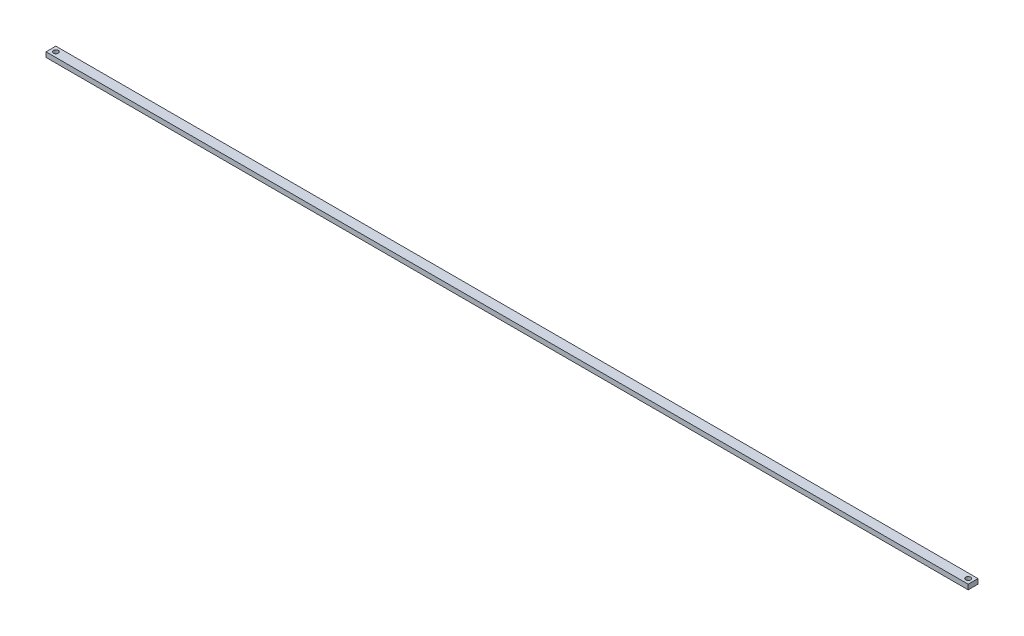
SolidWorks part; units mm, degrees
material "1060 Alloy"
ref_plane "Front Plane" through (0, 0, 0) normal (0, 0, 1) x (1, 0, 0)
ref_plane "Top Plane" through (0, 0, 0) normal (0, 1, 0) x (1, 0, 0)
ref_plane "Right Plane" through (0, 0, 0) normal (1, 0, 0) x (0, 0, -1)
sketch "Sketch1" plane through (0, 0, 0) normal (0, 1, 0) x (1, 0, 0)
  line L0 (0, -3.175) -> (596.9, -3.175) construction
  line L1 (0, 0) -> (596.9, 0)
  line L2 (0, 0) -> (0, -6.35)
  line L3 (0, -6.35) -> (596.9, -6.35)
  line L4 (596.9, 0) -> (596.9, -6.35)
  line L5 (298.45, -6.35) -> (298.45, 0) construction
  circle A0 centre (3.175, -3.175) radius 1.5875
  circle A1 centre (593.725, -3.175) radius 1.5875
  dimension "D3" = 3.175
  dimension "D4" = 3.175
  dimension "D1" = 596.9
  dimension "D2" = 6.35
extrude "Boss-Extrude1" add sketch "Sketch1" along normal blind 3.175
